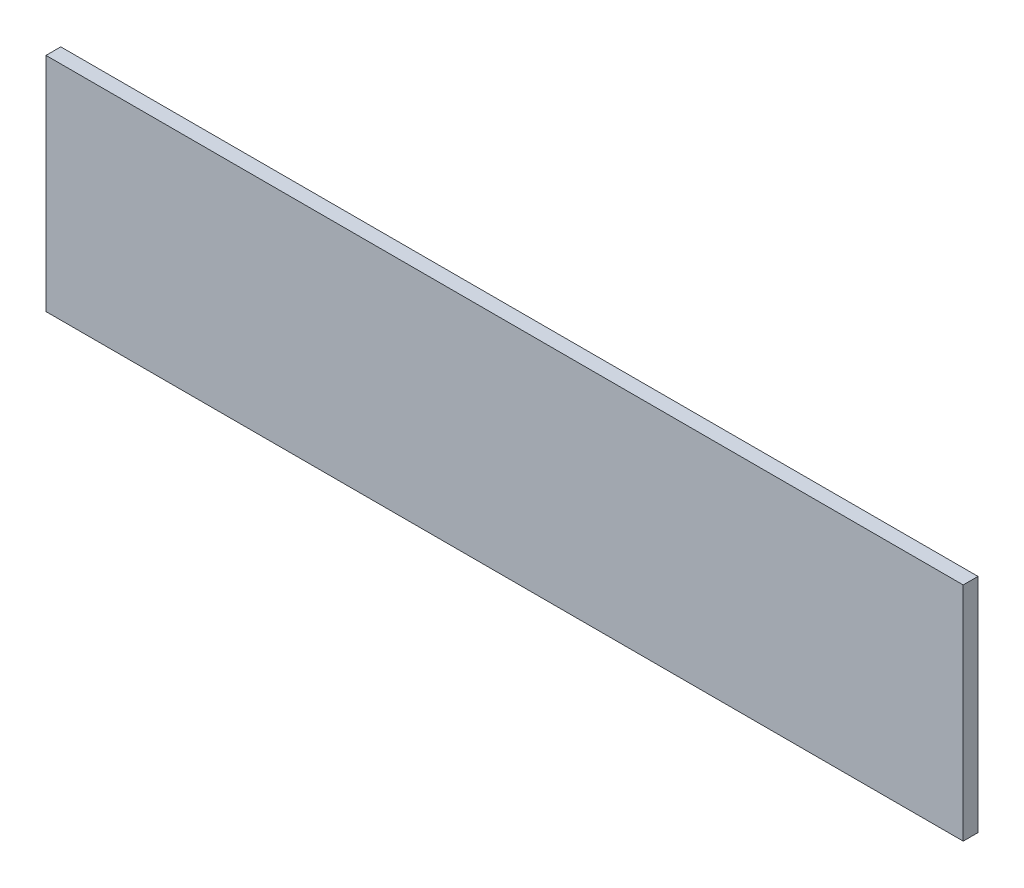
SolidWorks part; units mm, degrees
ref_plane "前视基准面" through (0, 0, 0) normal (0, 0, 1) x (1, 0, 0)
ref_plane "上视基准面" through (0, 0, 0) normal (0, 1, 0) x (1, 0, 0)
ref_plane "右视基准面" through (0, 0, 0) normal (1, 0, 0) x (0, 0, -1)
sketch "草图1" plane through (0, 0, 0) normal (0, 0, 1) x (1, 0, 0)
  line L1 (62, -15) -> (-62, -15)
  line L2 (62, -15) -> (62, 15)
  line L3 (62, 15) -> (-62, 15)
  line L4 (-62, -15) -> (-62, 15)
  line L5 (62, -15) -> (-62, 15) construction
  line L6 (62, 15) -> (-62, -15) construction
  point P0 (0, 0)
  dimension "D1" = 30
  dimension "D2" = 124
extrude "凸台-拉伸1" add sketch "草图1" along normal blind 2
